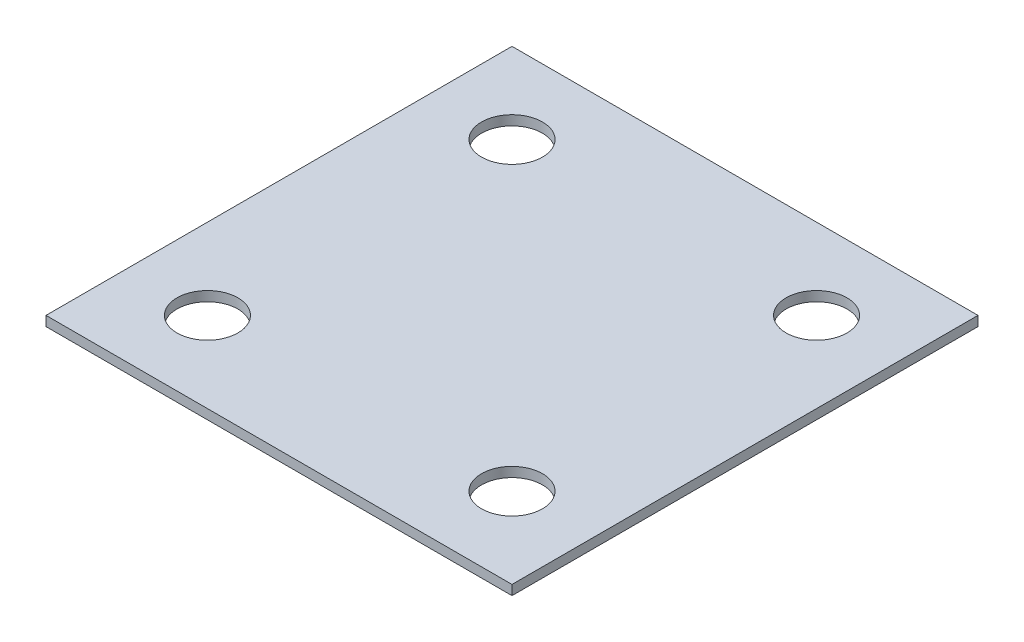
SolidWorks part; units mm, degrees
ref_plane "Front Plane" through (0, 0, 0) normal (0, 0, 1) x (1, 0, 0)
ref_plane "Top Plane" through (0, 0, 0) normal (0, 1, 0) x (1, 0, 0)
ref_plane "Right Plane" through (0, 0, 0) normal (1, 0, 0) x (0, 0, -1)
sketch "Sketch1" plane through (0, 0, 0) normal (0, 1, 0) x (1, 0, 0)
  line L1 (-382.5, 382.5) -> (382.5, 382.5)
  line L2 (-382.5, 382.5) -> (-382.5, -382.5)
  line L3 (-382.5, -382.5) -> (382.5, -382.5)
  line L4 (382.5, 382.5) -> (382.5, -382.5)
  line L5 (-382.5, 382.5) -> (382.5, -382.5) construction
  line L6 (-382.5, -382.5) -> (382.5, 382.5) construction
  point P0 (0, 0)
  dimension "D1" = 765
extrude "Boss-Extrude1" add sketch "Sketch1" along normal blind 16
sketch "Sketch3" [suppressed] plane through (-382.5, 0, 0) normal (-1, 0, 0) x (0, 0, 1)
  line L4 (-382.5, 0) -> (382.5, 0)
  line L5 (382.5, 0) -> (382.5, 16)
  line L6 (382.5, 16) -> (-382.5, 16)
  line L7 (-382.5, 16) -> (-382.5, 0)
  line L8 (-382.5, 0) -> (382.5, 0)
  line L9 (382.5, 0) -> (382.5, 16)
  line L10 (382.5, 16) -> (-382.5, 16)
  line L11 (-382.5, 16) -> (-382.5, 0)
  dimension "D1" = 0
extrude "Boss-Extrude2" [suppressed] add sketch "Sketch3" along normal blind 32
sketch "Sketch4" [suppressed] plane through (0, 16, 0) normal (0, 1, 0) x (1, 0, 0)
  line L0 (-382.5, 0) -> (382.5, 0) construction
  line L3 (-382.5, 382.5) -> (-382.5, -382.5) construction
  line L6 (382.5, -382.5) -> (382.5, 382.5) construction
  line L7 (-302.5, 382.5) -> (-302.5, -382.5) construction
  line L8 (382.5, 382.5) -> (-382.5, 382.5) construction
  line L9 (-382.5, -382.5) -> (382.5, -382.5) construction
  line L10 (-277.5, -310) -> (-277.5, -190)
  line L11 (-327.5, 310) -> (-277.5, 310)
  line L12 (-327.5, 310) -> (-327.5, 190)
  line L13 (-327.5, 190) -> (-277.5, 190)
  line L14 (-277.5, 310) -> (-277.5, 190)
  line L15 (-327.5, 310) -> (-277.5, 190) construction
  line L16 (-327.5, 190) -> (-277.5, 310) construction
  line L17 (-327.5, -310) -> (-277.5, -310)
  line L18 (-327.5, -310) -> (-327.5, -190)
  line L19 (-327.5, -190) -> (-277.5, -190)
  point P12 (-302.5, 250)
  dimension "D1" = 120
  dimension "D2" = 50
  dimension "D3" = 500
  dimension "D4" = 80
extrude "Cut-Extrude1" [suppressed] cut sketch "Sketch4" against normal up to next
sketch "Sketch5" plane through (0, 16, 0) normal (0, 1, 0) x (1, 0, 0)
  line L0 (0, 382.5) -> (0, -382.5) construction
  line L1 (382.5, 382.5) -> (-382.5, 382.5) construction
  line L2 (-382.5, -382.5) -> (382.5, -382.5) construction
  line L3 (-382.5, 250) -> (382.5, 250) construction
  line L4 (-382.5, 382.5) -> (-382.5, -382.5) construction
  line L5 (382.5, -382.5) -> (382.5, 382.5) construction
  line L6 (-382.5, 0) -> (382.5, 0) construction
  line L7 (-250, 250) -> (-250, 382.5) construction
  line L8 (-250, 200) -> (-382.5, 200) construction
  circle A0 centre (-250, 250) radius 50
  circle A1 centre (250, 250) radius 50
  circle A2 centre (250, -250) radius 50
  circle A3 centre (-250, -250) radius 50
  dimension "D1" = 100
  dimension "D2" = 500
extrude "Cut-Extrude2" cut sketch "Sketch5" against normal up to next
sketch "Sketch6" [suppressed] plane through (0, 16, 0) normal (0, 1, 0) x (1, 0, 0)
  line L0 (-16, 382.5) -> (-16, -382.5) construction
  line L1 (382.5, 382.5) -> (-414.5, 382.5) construction
  line L2 (-414.5, -382.5) -> (382.5, -382.5) construction
  line L3 (-414.5, 0) -> (382.5, 0) construction
  line L4 (-414.5, -382.5) -> (-414.5, 382.5) construction
  line L5 (382.5, -382.5) -> (382.5, 382.5) construction
  line L6 (-414.5, 250) -> (382.5, 250) construction
  line L7 (-266, 250) -> (-266, -250) construction
  line L8 (-266, -250) -> (234, -250) construction
  circle A0 centre (-266, 250) radius 50
  circle A1 centre (234, 250) radius 50
  circle A2 centre (234, -250) radius 50
  circle A3 centre (-266, -250) radius 50
  dimension "D1" = 100
  dimension "D2" = 500
extrude "Cut-Extrude3" [suppressed] cut sketch "Sketch6" against normal up to next
fillet "Fillet1" [suppressed] radius 10
